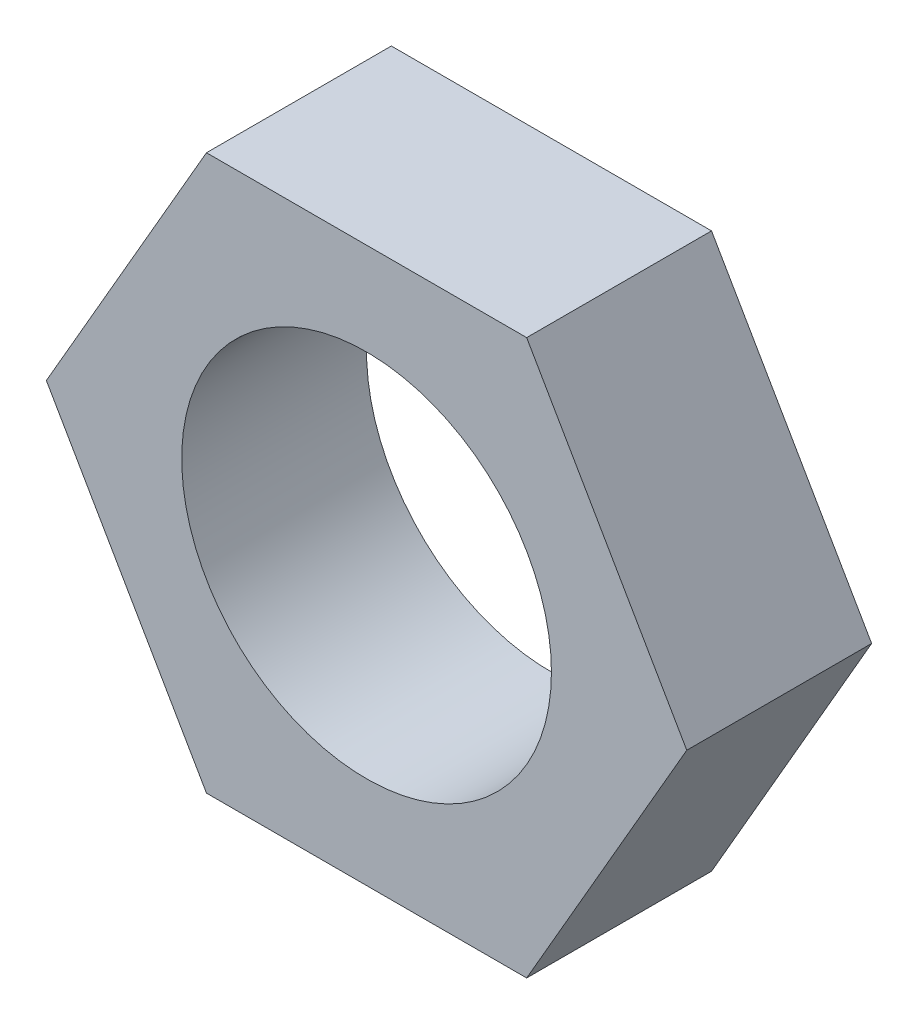
SolidWorks part; units mm, degrees
ref_plane "Front Plane" through (0, 0, 0) normal (0, 0, 1) x (1, 0, 0)
ref_plane "Top Plane" through (0, 0, 0) normal (0, 1, 0) x (1, 0, 0)
ref_plane "Right Plane" through (0, 0, 0) normal (1, 0, 0) x (0, 0, -1)
sketch "Sketch1" plane through (0, 0, 0) normal (0, 0, 1) x (1, 0, 0)
  line L1 (5.4993, -9.525) -> (10.9985, 0)
  line L2 (10.9985, 0) -> (5.4993, 9.525)
  line L3 (5.4993, 9.525) -> (-5.4993, 9.525)
  line L4 (-5.4993, 9.525) -> (-10.9985, 0)
  line L5 (-10.9985, 0) -> (-5.4993, -9.525)
  line L6 (-5.4993, -9.525) -> (5.4993, -9.525)
  circle A0 centre (0, 0) radius 9.525 construction
  circle A1 centre (0, 0) radius 6.35
  dimension "D3" = 12.7
  dimension "D1" = 19.05
extrude "Boss-Extrude1" add sketch "Sketch1" along normal blind 6.35
